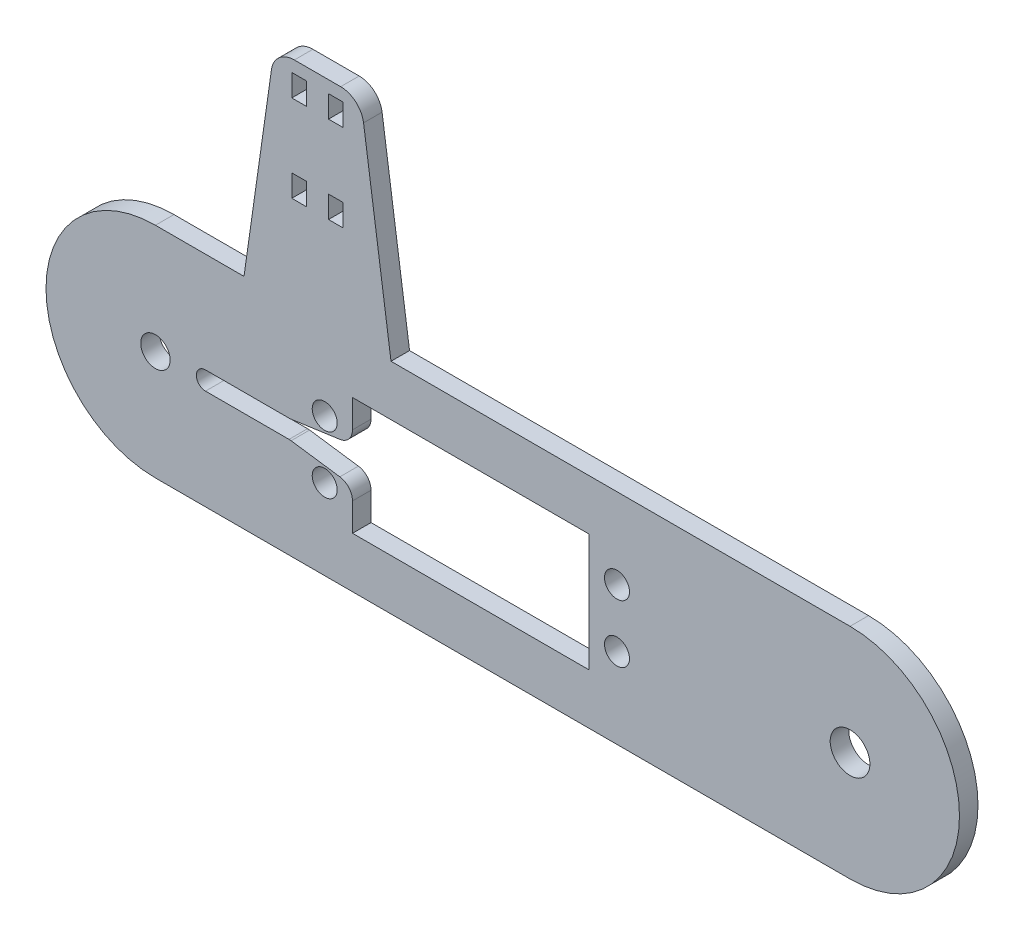
SolidWorks part; units mm, degrees
ref_plane "Front Plane" through (0, 0, 0) normal (0, 0, 1) x (1, 0, 0)
ref_plane "Top Plane" through (0, 0, 0) normal (0, 1, 0) x (1, 0, 0)
ref_plane "Right Plane" through (0, 0, 0) normal (1, 0, 0) x (0, 0, -1)
sketch "Sketch1" plane through (0, 0, 0) normal (0, 0, 1) x (1, 0, 0)
  line L8 (0, 18.9078) -> (120.015, 18.9078) construction
  line L18 (120.015, 37.8155) -> (0, 37.8155)
  line L37 (0, 0) -> (120.015, 0)
  line L42 (120.015, 37.8155) -> (120.015, 0) construction
  line L43 (0, 37.8155) -> (0, 0) construction
  line L55 (60.0075, 37.8155) -> (60.0075, 18.9078) construction
  circle A21 centre (120.015, 18.9078) radius 3.429
  circle A22 centre (0, 18.9078) radius 2.54
  arc A25 (120.015, 37.8155) -> (120.015, 0) centre (120.015, 18.9078) cw
  arc A26 (0, 0) -> (0, 37.8155) centre (0, 18.9078) cw
  dimension "D5" = 18.9078
  dimension "D2" = 5.08
  dimension "D1" = 6.858
  dimension "D7" = 120.015
extrude "Boss-Extrude1" add sketch "Sketch1" along normal blind 3.2004
sketch "Sketch5" plane through (0, 0, 0) normal (0, 0, -1) x (-1, 0, 0)
  line L0 (0, 18.9078) -> (-120.015, 18.9078) construction
  line L6 (-74.944, 29.0678) -> (-74.944, 8.7478)
  line L7 (-34.05, 29.0678) -> (-34.05, 8.7478)
  line L12 (-54.497, 29.0678) -> (-54.497, 8.7478) construction
  line L13 (-79.747, 13.9078) -> (-79.747, 23.9078) construction
  line L14 (-29.247, 13.9078) -> (-29.247, 23.9078) construction
  line L15 (-79.747, 18.9078) -> (-29.247, 18.9078) construction
  line L21 (-74.944, 8.7478) -> (-34.05, 8.7478)
  line L25 (-74.944, 29.0678) -> (-34.05, 29.0678)
  circle A0 centre (-79.747, 23.9078) radius 2.159
  circle A1 centre (-29.247, 13.9078) radius 2.159
  circle A2 centre (-29.247, 23.9078) radius 2.159
  circle A3 centre (-79.747, 13.9078) radius 2.159
  circle A5 centre (0, 18.9078) radius 2.54 construction
  point P6 (-44.45, 18.9078)
  point P9 (-54.497, 18.9078)
  dimension "D2" = 4.318
  dimension "D3" = 40.894
  dimension "D1" = 50.5
  dimension "D4" = 20.32
  dimension "D5" = 10.4
  dimension "D6" = 44.45
  dimension "D7" = 10
extrude "Cut-Extrude3" cut sketch "Sketch5" against normal through all
sketch "Sketch6" plane through (0, 0, 3.2004) normal (0, 0, 1) x (1, 0, 0)
  line L0 (16.905, 18.9078) -> (34.05, 18.9078) construction
  line L1 (8.65, 20.4953) -> (25.16, 20.4953)
  line L2 (8.65, 20.4953) -> (8.65, 17.3203) construction
  line L3 (8.65, 17.3203) -> (25.16, 17.3203)
  line L4 (25.16, 20.4953) -> (25.16, 17.3203) construction
  line L5 (34.05, 8.7478) -> (34.05, 29.0678) construction
  line L6 (16.905, 20.4953) -> (16.905, 17.3203) construction
  arc A0 (8.65, 20.4953) -> (8.65, 17.3203) centre (8.65, 18.9078) ccw
  arc A1 (25.16, 20.4953) -> (25.16, 17.3203) centre (25.16, 18.9078) cw
  dimension "D1" = 25.4
  dimension "D2" = 3.175
  dimension "D3" = 16.51
extrude "Cut-Extrude4" cut sketch "Sketch6" against normal up to surface (3.2004 mm away) up to face at (77.588, 23.9078, 0)
sketch "Sketch8" plane through (0, 0, 3.2004) normal (0, 0, 1) x (1, 0, 0)
  line L0 (28.208, 21.1938) -> (28.208, 16.6218) construction
  line L1 (34.05, 15.7963) -> (34.05, 22.0193)
  line L2 (34.05, 15.7963) -> (23.2648, 17.3203)
  line L4 (34.05, 22.0193) -> (23.2648, 20.4953)
  line L5 (34.05, 18.9078) -> (28.208, 18.9078) construction
  line L6 (34.05, 8.7478) -> (34.05, 29.0678) construction
  line L8 (25.16, 20.4953) -> (8.65, 20.4953) construction
  line L9 (8.65, 17.3203) -> (25.16, 17.3203) construction
  line L10 (23.2648, 20.4953) -> (23.2648, 17.3203)
  point P4 (34.05, 18.9078)
  dimension "D1" = 6.223
  dimension "D2" = 4.572
  dimension "D3" = 5.842
extrude "Cut-Extrude5" cut sketch "Sketch8" against normal up to surface (3.2004 mm away) up to face at (16.905, 18.9078, 0)
sketch "Sketch9" plane through (0, 0, 0) normal (0, 0, -1) x (-1, 0, 0)
  line L0 (-120.015, 37.8155) -> (0, 37.8155) construction
  line L3 (-40.7035, 37.8155) -> (-15.3035, 37.8155)
  line L5 (-28.0035, 74.5517) -> (-28.0035, 37.8155) construction
  line L6 (-31.1785, 55.5335) -> (-24.8285, 55.5335) construction
  line L7 (-28.0035, 37.8155) -> (-28.0035, 18.9078) construction
  line L8 (-31.1785, 53.6285) -> (-31.1785, 57.4385) construction
  line L9 (-32.4485, 53.6285) -> (-32.4485, 57.4385)
  line L10 (-32.4485, 53.6285) -> (-29.9085, 53.6285)
  line L11 (-29.9085, 53.6285) -> (-29.9085, 57.4385)
  line L12 (-32.4485, 57.4385) -> (-29.9085, 57.4385)
  line L13 (-24.8285, 53.6285) -> (-24.8285, 57.4385) construction
  line L14 (-26.0985, 53.6285) -> (-26.0985, 57.4385)
  line L15 (-26.0985, 53.6285) -> (-23.5585, 53.6285)
  line L16 (-23.5585, 53.6285) -> (-23.5585, 57.4385)
  line L17 (-26.0985, 57.4385) -> (-23.5585, 57.4385)
  line L18 (-32.004, 74.5517) -> (-24.003, 74.5517)
  line L25 (-31.1785, 70.5546) -> (-24.8285, 70.5546) construction
  line L26 (-28.208, 18.9078) -> (-28.0035, 18.9078) construction
  line L27 (-31.1785, 68.6496) -> (-31.1785, 72.4596) construction
  line L28 (-35.9612, 71.1181) -> (-40.7035, 37.8155)
  line L29 (-20.0458, 71.1181) -> (-15.3035, 37.8155)
  line L30 (-28.208, 21.1938) -> (-28.208, 16.6218) construction
  line L31 (-32.4485, 68.6496) -> (-32.4485, 72.4596)
  line L32 (-32.4485, 68.6496) -> (-29.9085, 68.6496)
  line L33 (-29.9085, 68.6496) -> (-29.9085, 72.4596)
  line L34 (-32.4485, 72.4596) -> (-29.9085, 72.4596)
  line L35 (-24.8285, 68.6496) -> (-24.8285, 72.4596) construction
  line L36 (-26.0985, 68.6496) -> (-26.0985, 72.4596)
  line L37 (-26.0985, 68.6496) -> (-23.5585, 68.6496)
  line L38 (-23.5585, 68.6496) -> (-23.5585, 72.4596)
  line L39 (-26.0985, 72.4596) -> (-23.5585, 72.4596)
  arc A3 (-32.004, 74.5517) -> (-35.9612, 71.1181) centre (-32.004, 70.5546) ccw
  arc A6 (-24.003, 74.5517) -> (-20.0458, 71.1181) centre (-24.003, 70.5546) cw
  point P1 (0, 0)
  point P12 (-28.0035, 55.5335)
  point P27 (-28.0035, 70.5546)
  point P43 (-28.0035, 70.5546)
  dimension "D7" = 3.9971
  dimension "D1" = 25.4
  dimension "D2" = 36.7362
  dimension "D3" = 16.209
  dimension "D4" = 3.81
  dimension "D5" = 2.54
  dimension "D6" = 6.35
  dimension "D8" = 15.0211
  dimension "D10" = 0.2045
extrude "Boss-Extrude2" add sketch "Sketch9" against normal up to surface (3.2004 mm away) up to face at (77.588, 23.9078, 3.2004)
fillet "Fillet1" radius 2.54 4 edges at (23.2648, 20.4953, 1.6002) (34.05, 22.0193, 1.6002) (34.05, 15.7963, 1.6002) (23.2648, 17.3203, 1.6002)
